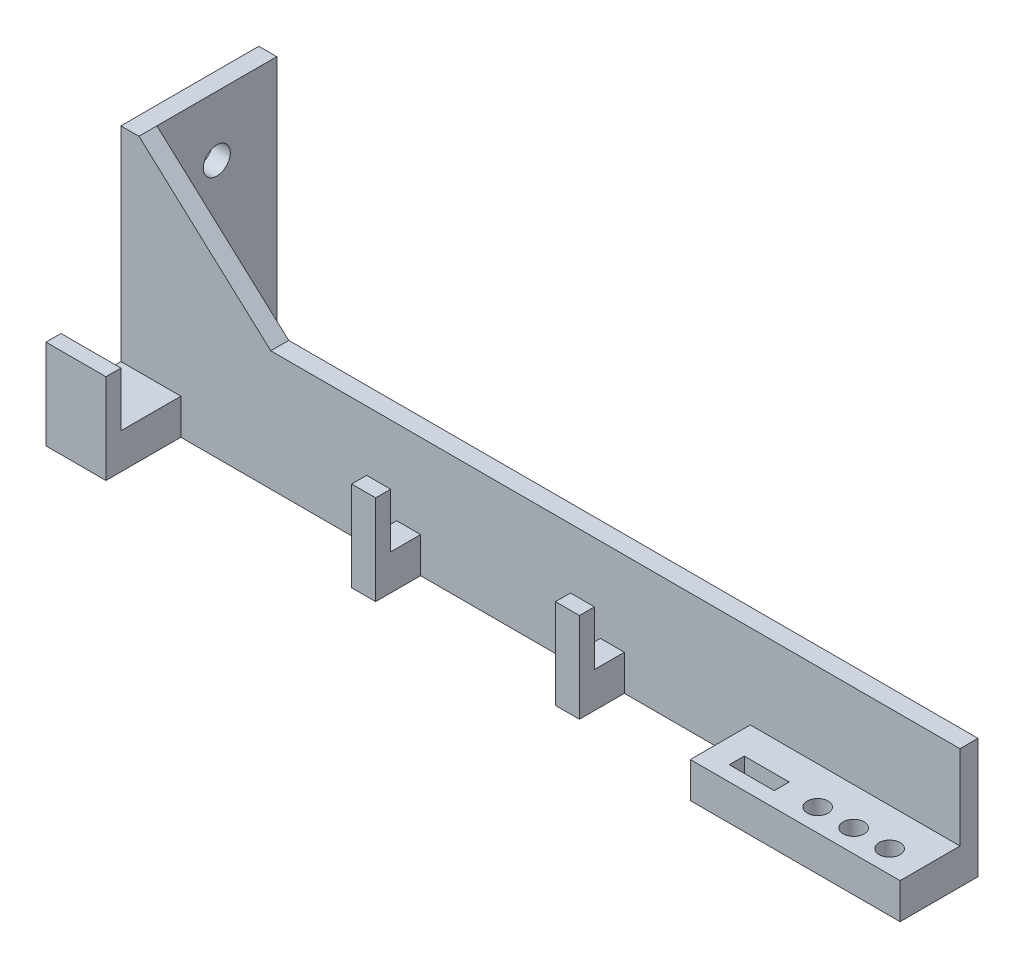
SolidWorks part; units mm, degrees
ref_plane "Front Plane" through (0, 0, 0) normal (0, 0, 1) x (1, 0, 0)
ref_plane "Top Plane" through (0, 0, 0) normal (0, 1, 0) x (1, 0, 0)
ref_plane "Right Plane" through (0, 0, 0) normal (1, 0, 0) x (0, 0, -1)
sketch "Sketch1" plane through (0, 0, 0) normal (1, 0, 0) x (0, 0, -1)
  line L7 (0, -33) -> (3, -33)
  line L8 (3, -13) -> (3, -33)
  line L9 (3, -13) -> (0, -13)
  line L10 (0, -13) -> (0, -33)
  dimension "D4" = 3
  dimension "D5" = 20
extrude "Boss-Extrude1" add sketch "Sketch1" along normal blind 140
sketch "Sketch3" plane through (0, 0, 0) normal (0, 0, 1) x (1, 0, 0)
  line L1 (0, -33) -> (10, -33)
  line L2 (0, -33) -> (0, -27.0594)
  line L3 (0, -27.0594) -> (10, -27.0594)
  line L4 (10, -33) -> (10, -27.0594)
  line L5 (50, -33) -> (46, -33)
  line L6 (50, -33) -> (50, -27.0594)
  line L7 (50, -27.0594) -> (46, -27.0594)
  line L8 (46, -33) -> (46, -27.0594)
  line L10 (80, -33) -> (84, -33)
  line L11 (80, -33) -> (80, -27.0594)
  line L12 (80, -27.0594) -> (84, -27.0594)
  line L13 (84, -33) -> (84, -27.0594)
  line L14 (105, -33) -> (140, -33)
  line L15 (105, -33) -> (105, -27.0594)
  line L16 (105, -27.0594) -> (140, -27.0594)
  line L17 (140, -33) -> (140, -27.0594)
  dimension "D1" = 10
  dimension "D3" = 4
  dimension "D4" = 30
  dimension "D5" = 4
  dimension "D6" = 25
extrude "Boss-Extrude2" add sketch "Sketch3" along normal blind 10
sketch "Sketch5" plane through (0, -33, 0) normal (0, -1, 0) x (1, 0, 0)
  line L0 (84, 10) -> (84, 0) construction
  line L1 (46, 10) -> (84, 10)
  line L2 (46, 10) -> (46, 5)
  line L3 (46, 5) -> (84, 5)
  line L4 (84, 10) -> (84, 5)
extrude "Cut-Extrude2" cut sketch "Sketch5" against normal blind 15
sketch "Sketch6" plane through (0, -33, 0) normal (0, -1, 0) x (1, 0, 0)
  line L0 (10, 10) -> (10, 0) construction
  line L1 (0, 10) -> (10, 10)
  line L2 (0, 10) -> (0, 12.5)
  line L3 (0, 12.5) -> (10, 12.5)
  line L4 (10, 10) -> (10, 12.5)
  line L5 (46, 5) -> (50, 5)
  line L6 (46, 5) -> (46, 7.5)
  line L7 (46, 7.5) -> (50, 7.5)
  line L8 (50, 5) -> (50, 7.5)
  line L9 (80, 5) -> (84, 5)
  line L10 (80, 5) -> (80, 7.5)
  line L11 (80, 7.5) -> (84, 7.5)
  line L12 (84, 5) -> (84, 7.5)
  line L13 (50, 5) -> (50, 0) construction
  line L14 (84, 5) -> (84, 0) construction
  dimension "D1" = 2.5
extrude "Boss-Extrude4" add sketch "Sketch6" against normal blind 15
sketch "Sketch7" plane through (0, -27.0594, 0) normal (0, 1, 0) x (1, 0, 0)
  line L0 (140, -10) -> (105, -10) construction
  line L1 (109, -5) -> (116.5, -5)
  line L2 (109, -5) -> (109, -7.5)
  line L3 (109, -7.5) -> (116.5, -7.5)
  line L4 (116.5, -5) -> (116.5, -7.5)
  line L5 (105, -10) -> (105, 0) construction
  circle A0 centre (128.5, -6.25) radius 1.75
  circle A1 centre (122.5, -6.25) radius 1.75
  circle A2 centre (134.5, -6.25) radius 1.75
  point P13 (116.5, -6.25)
  dimension "D1" = 3.5
  dimension "D7" = 6
  dimension "D8" = 3.5
  dimension "D9" = 6
  dimension "D2" = 2.5
  dimension "D3" = 4
  dimension "D4" = 7.5
  dimension "D5" = 2.5
  dimension "D6" = 6
extrude "Cut-Extrude3" cut sketch "Sketch7" against normal blind 15
sketch "Sketch8" plane through (0, 0, 0) normal (0, 0, 1) x (1, 0, 0)
  line L0 (0, -13) -> (0, -27.0594) construction
  line L1 (140, -13) -> (140, -27.0594) construction
  line L2 (140, -13) -> (0, -13) construction
  circle A0 centre (20, -23) radius 2.25
  circle A1 centre (120, -23) radius 2.25
  dimension "D1" = 20
  dimension "D2" = 20
  dimension "D3" = 10
  dimension "D4" = 10
  dimension "D5" = 4.5
  dimension "D6" = 4.5
sketch "Sketch9" plane through (0, 0, 0) normal (-1, 0, 0) x (0, 0, 1)
  line L0 (12.5, -33) -> (-3, -33) construction
  line L1 (-3, 7) -> (-23, 7)
  line L2 (-3, 7) -> (-3, -33)
  line L3 (-3, -33) -> (-23, -33)
  line L4 (-23, 7) -> (-23, -33)
  circle A0 centre (-13, -3) radius 2.25
  point P9 (0, 0)
  point P10 (-13, 7)
  dimension "D3" = 10
  dimension "D4" = 4.5
  dimension "D1" = 20
  dimension "D2" = 40
extrude "Boss-Extrude5" add sketch "Sketch9" against normal blind 3
sketch "Sketch10" plane through (0, 0, 0) normal (0, 0, 1) x (1, 0, 0)
  line L0 (0, 7) -> (3, 7)
  line L1 (3, 7) -> (25, -13)
  line L2 (140, -13) -> (0, -13) construction
  line L3 (25, -13) -> (0, -13)
  line L4 (0, -13) -> (0, 7)
  dimension "D1" = 25
extrude "Boss-Extrude6" add sketch "Sketch10" against normal up to surface (3 mm away) up to face at (1.5, -3, -3)
